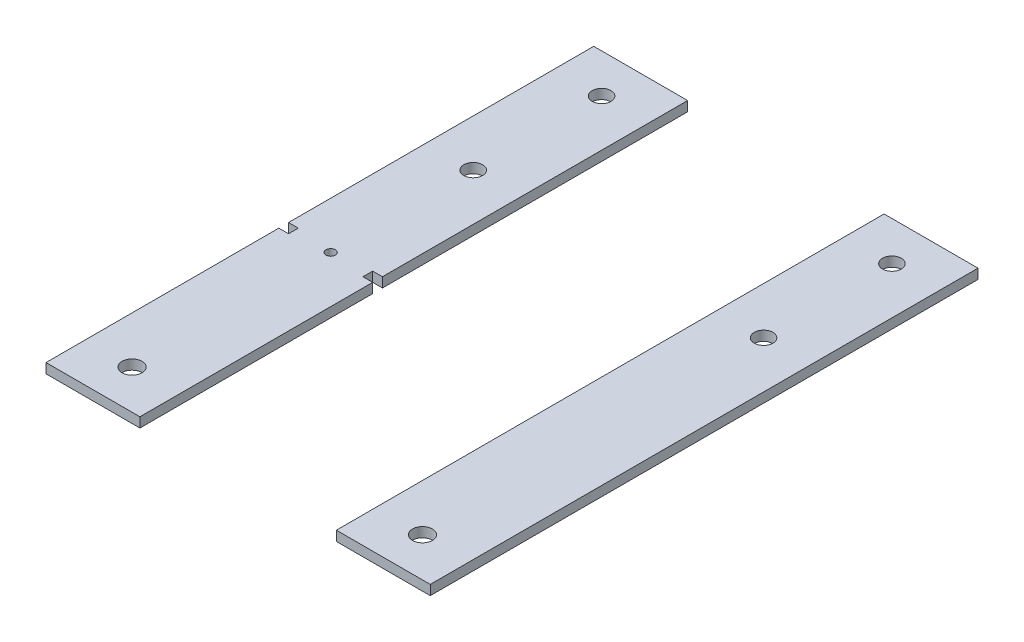
SolidWorks part; units mm, degrees
ref_plane "Front Plane" through (0, 0, 0) normal (0, 0, 1) x (1, 0, 0)
ref_plane "Top Plane" through (0, 0, 0) normal (0, 1, 0) x (1, 0, 0)
ref_plane "Right Plane" through (0, 0, 0) normal (1, 0, 0) x (0, 0, -1)
sketch "Sketch1" plane through (0, 0, 0) normal (0, 1, 0) x (1, 0, 0)
  line L0 (0, -1000) -> (0, 49000) construction
  line L1 (-31.885, 88.9) -> (-31.885, -10.16)
  line L2 (-31.885, -88.9) -> (-62.365, -88.9)
  line L3 (-31.885, 88.9) -> (-62.365, 88.9)
  line L4 (62.365, 88.9) -> (62.365, -88.9)
  line L5 (-62.365, 88.9) -> (-62.365, -10.16)
  line L6 (31.885, 88.9) -> (62.365, 88.9)
  line L7 (-62.365, -10.16) -> (-59.19, -10.16)
  line L8 (31.885, -88.9) -> (62.365, -88.9)
  line L9 (31.885, 88.9) -> (31.885, -88.9)
  line L10 (-59.19, -10.16) -> (-59.19, -13.335)
  line L11 (-59.19, -13.335) -> (-62.365, -13.335)
  line L12 (-31.885, -13.335) -> (-35.06, -13.335)
  line L13 (-35.06, -13.335) -> (-35.06, -10.16)
  line L14 (-35.06, -10.16) -> (-31.885, -10.16)
  line L16 (-62.365, -13.335) -> (-62.365, -88.9)
  line L18 (-31.885, -13.335) -> (-31.885, -88.9)
  circle A0 centre (-47.125, -11.7475) radius 1.524
  circle A1 centre (47.125, 76.2) radius 3.048
  circle A2 centre (-47.125, 34.5293) radius 3.048
  circle A3 centre (47.125, 34.5293) radius 3.048
  circle A5 centre (-47.125, 76.2) radius 3.048
  circle A6 centre (47.125, -76.2) radius 3.2385
  circle A7 centre (-47.125, -76.2) radius 3.2385
  point P2 (47.125, 88.9)
  point P11 (62.365, 0)
  point P29 (-35.06, -11.7475)
  dimension "D5" = 12.7
  dimension "D6" = 6.096
  dimension "D8" = 3.175
  dimension "D10" = 6.477
  dimension "D11" = 3.048
  dimension "D1" = 177.8
  dimension "D2" = 30.48
  dimension "D3" = 94.25
  dimension "D4" = 78.74
  dimension "D7" = 41.6707
  dimension "D9" = 3.175
  dimension "D12" = 12.7
extrude "Boss-Extrude1" add sketch "Sketch1" along normal blind 3.175
